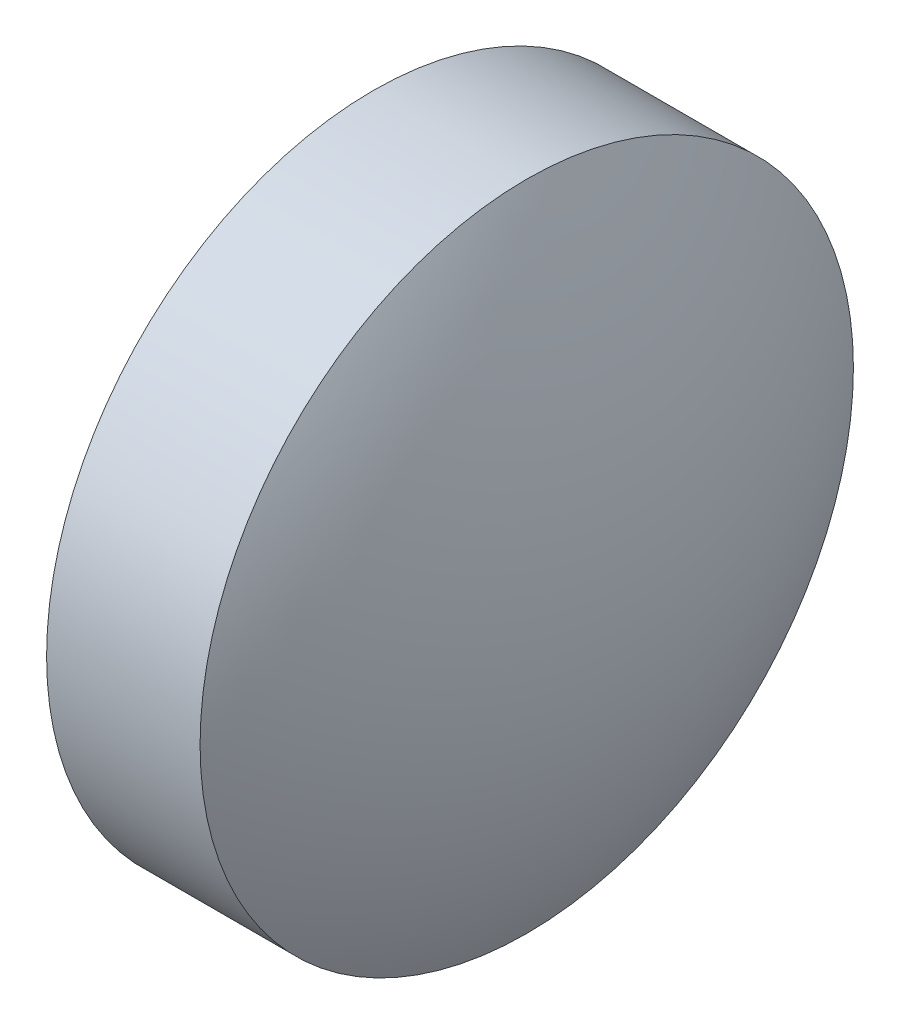
SolidWorks part; units mm, degrees
ref_plane "前视基准面" through (0, 0, 0) normal (0, 0, 1) x (1, 0, 0)
ref_plane "上视基准面" through (0, 0, 0) normal (0, 1, 0) x (1, 0, 0)
ref_plane "右视基准面" through (0, 0, 0) normal (1, 0, 0) x (0, 0, -1)
sketch "草图1" plane through (0, 0, 0) normal (0, 0, 1) x (1, 0, 0)
  line L0 (531.4519, 77.2205) -> (537.5873, 77.2205) construction
  line L1 (532.3135, 77.2205) -> (532.3135, 80.3705)
  line L2 (534.6135, 77.2205) -> (532.3135, 77.2205)
  line L5 (532.3135, 80.3705) -> (533.7935, 80.3705)
  arc A0 (534.6135, 77.2205) -> (533.7935, 80.3705) centre (528.1532, 77.2205) ccw
revolve "旋转1" add sketch "草图1" angle 360 about L0
